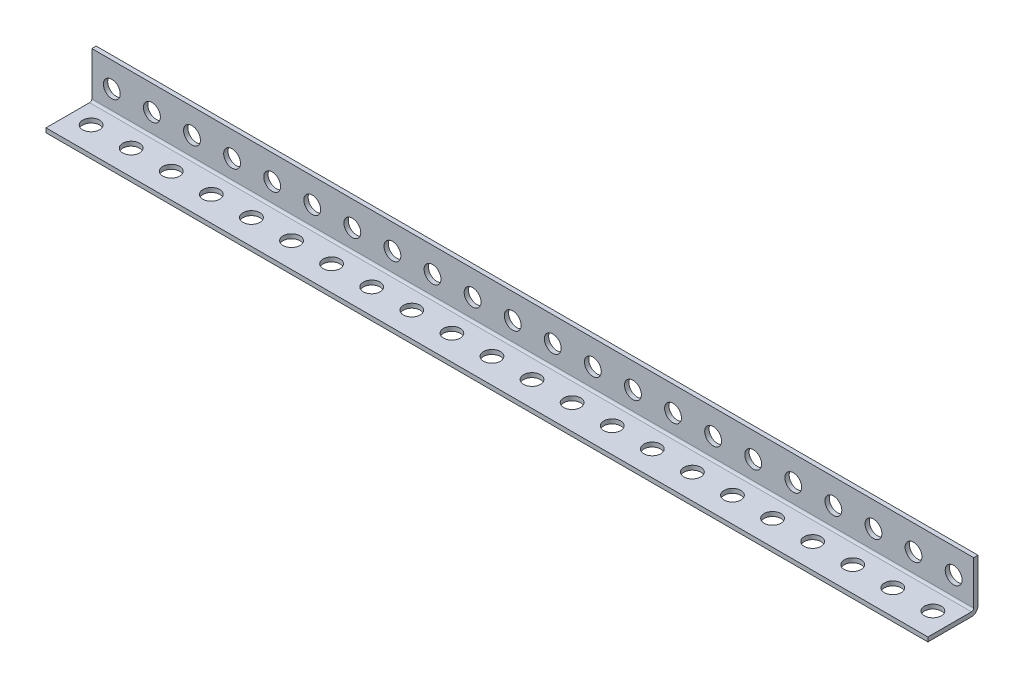
SolidWorks part; units mm, degrees
material "6061-T6 (SS)"
ref_plane "Front Plane" through (0, 0, 0) normal (0, 0, 1) x (1, 0, 0)
ref_plane "Top Plane" through (0, 0, 0) normal (0, 1, 0) x (1, 0, 0)
ref_plane "Right Plane" through (0, 0, 0) normal (1, 0, 0) x (0, 0, -1)
sketch "Sketch1" plane through (0, 0, 0) normal (1, 0, 0) x (0, 0, -1)
  line L0 (-15.875, -13.1318) -> (13.1318, -13.1318) construction
  line L1 (13.1318, -13.1318) -> (13.1318, 15.875) construction
  line L2 (13.1318, 15.875) -> (15.875, 15.875) construction
  line L3 (15.875, 15.875) -> (15.875, -15.875) construction
  line L4 (15.875, -15.875) -> (-15.875, -15.875) construction
  line L5 (-15.875, -15.875) -> (-15.875, -13.1318) construction
  line L6 (0, -15.875) -> (0, 15.875) construction
  line L7 (15.875, 0) -> (-15.875, 0) construction
  dimension "Thickness | T" = 2.7432
  dimension "Width (A)" = 31.75
  dimension "Width (B)" = 31.75
sketch "Sketch2" plane through (0, 0, 0) normal (0, 0, 1) x (1, 0, 0)
  line L0 (-609.6, 0) -> (609.6, 0) construction
  line L1 (-609.6, 15.875) -> (609.6, 15.875) construction
  line L2 (-609.6, 15.875) -> (-609.6, -15.875) construction
  line L3 (-609.6, -15.875) -> (609.6, -15.875) construction
  line L4 (609.6, 15.875) -> (609.6, -15.875) construction
  line L5 (0, 15.875) -> (0, -15.875) construction
  line L7 (-609.6, -13.1318) -> (609.6, -13.1318) construction
  circle A0 centre (596.9, 0) radius 5.334 construction
  circle A1 centre (571.5, 0) radius 5.334 construction
  point P15 (533.4, 0)
  point P16 (-533.4, 0)
  point P24 (602.234, 0)
  dimension "Mounting Hole Diameter" = 10.668
  dimension "Length | L" = 1219.2
  dimension "Mounting Hole Center to Center" = 25.4
  dimension "D1" = 12.7
  dimension "D2" = 63.5
sketch "Sketch3" plane through (0, 0, 0) normal (0, 1, 0) x (1, 0, 0)
  line L1 (-609.6, 15.875) -> (609.6, 15.875) construction
  line L2 (-609.6, 15.875) -> (-609.6, -15.875) construction
  line L3 (-609.6, -15.875) -> (609.6, -15.875) construction
  line L4 (609.6, 15.875) -> (609.6, -15.875) construction
  line L5 (-609.6, 13.1318) -> (609.6, 13.1318) construction
  line L7 (-609.6, 0) -> (609.6, 0) construction
  circle A0 centre (596.9, 0) radius 5.334 construction
  circle A1 centre (571.5, 0) radius 5.334 construction
  point P19 (-533.4, 0)
  point P21 (602.234, 0)
  point P22 (533.4, 0)
sketch "Sketch4" plane through (0, 0, 0) normal (1, 0, 0) x (0, 0, -1)
  line L0 (-15.875, -13.1318) -> (11.7602, -13.1318)
  line L1 (13.1318, -11.7602) -> (13.1318, 15.875)
  line L2 (13.1318, 15.875) -> (15.875, 15.875)
  line L3 (15.875, 15.875) -> (15.875, -11.7602)
  line L4 (11.7602, -15.875) -> (-15.875, -15.875)
  line L5 (-15.875, -15.875) -> (-15.875, -13.1318)
  line L6 (11.7602, -13.1318) -> (11.7602, -10.3886) construction
  arc A0 (11.7602, -13.1318) -> (13.1318, -11.7602) centre (11.7602, -11.7602) ccw
  arc A1 (15.875, -11.7602) -> (11.7602, -15.875) centre (11.7602, -11.7602) cw
extrude "Boss-Extrude1" add sketch "Sketch4" along normal up to vertex (609.6 mm away) and the other way up to vertex (609.6 mm away) up to point (609.6, 0, 0) other way up to point (-609.6, 0, 0)
sketch "Sketch5" plane through (0, 0, 0) normal (0, 0, 1) x (1, 0, 0)
  circle A0 centre (596.9, 0) radius 5.334
extrude "Cut-Extrude1" cut sketch "Sketch5" against normal through all
sketch "Sketch6" plane through (0, 0, 0) normal (0, 1, 0) x (1, 0, 0)
  circle A0 centre (596.9, 0) radius 5.334
extrude "Cut-Extrude2" cut sketch "Sketch6" against normal through all
pattern_linear "LPattern1" count 48 spacing 25.4 along (-1, 0, 0) of "Cut-Extrude2", "Cut-Extrude1"
sketch "Sketch7" plane through (0, 0, -15.875) normal (0, 0, -1) x (-1, 0, 0)
  line L0 (-609.6, -15.875) -> (609.6, -15.875) construction
  line L1 (-609.6, 15.875) -> (25.4, 15.875)
  line L2 (-609.6, 15.875) -> (-609.6, -15.875)
  line L3 (-609.6, -15.875) -> (25.4, -15.875)
  line L4 (25.4, 15.875) -> (25.4, -15.875)
  line L5 (602.234, 0) -> (609.6, 0) construction
  line L6 (609.6, -11.7602) -> (609.6, 15.875) construction
  line L7 (32.766, 0) -> (25.4, 0)
  circle A0 centre (596.9, 0) radius 5.334 construction
  circle A1 centre (38.1, 0) radius 5.334 construction
  dimension "D1" = 7.366
extrude "Cut-Extrude3" cut sketch "Sketch7" against normal blind 70 contours L4 L1 L2 L3
sketch "Sketch8" plane through (0, 0, -15.875) normal (0, 0, -1) x (-1, 0, 0)
  line L0 (25.4, -15.875) -> (609.6, -15.875) construction
  line L1 (25.4, 15.875) -> (50.8, 15.875)
  line L2 (25.4, 15.875) -> (25.4, -15.875)
  line L3 (25.4, -15.875) -> (50.8, -15.875)
  line L4 (50.8, 15.875) -> (50.8, -15.875)
  line L6 (58.166, 0) -> (50.8, 0)
  circle A0 centre (63.5, 0) radius 5.334 construction
  circle M28 centre (38.1, 0) radius 5.334
  line M29 (25.4, 15.875) -> (25.4, -11.7602)
  line M30 (25.4, -11.7602) -> (609.6, -11.7602)
  line M32 (609.6, 15.875) -> (25.4, 15.875)
  dimension "D1" = 7.366
extrude "Cut-Extrude4" cut sketch "Sketch8" against normal blind 70 contours L4 M32 M29 M30 M28 | L4 L2 L3 M30
sketch "Sketch9" plane through (0, 0, -15.875) normal (0, 0, -1) x (-1, 0, 0)
  line L0 (602.234, 0) -> (609.6, 0)
  line L1 (609.6, -11.7602) -> (609.6, 15.875) construction
  line L2 (596.9, 5.334) -> (596.9, 15.875)
  line L3 (50.8, 15.875) -> (609.6, 15.875) construction
  line L4 (58.166, 0) -> (50.8, 0)
  line L5 (50.8, 15.875) -> (50.8, -11.7602) construction
  line L6 (63.5, 5.334) -> (63.5, 15.875)
  circle A0 centre (596.9, 0) radius 5.334 construction
  circle A1 centre (63.5, 0) radius 5.334 construction
sketch "Sketch10" plane through (0, -15.875, 0) normal (0, -1, 0) x (1, 0, 0)
  line L0 (-58.166, 0) -> (-50.8, 0)
  line L1 (-50.8, 15.875) -> (-50.8, -11.7602) construction
  line L2 (-63.5, 5.334) -> (-63.5, 15.875)
  line L3 (-50.8, 15.875) -> (-609.6, 15.875) construction
  line L4 (-602.234, 0) -> (-609.6, 0)
  line L5 (-609.6, 15.875) -> (-609.6, -11.7602) construction
  line L6 (-596.9, 5.334) -> (-596.9, 15.875)
  circle A0 centre (-63.5, 0) radius 5.334 construction
  circle A1 centre (-596.9, 0) radius 5.334 construction
equation "\"D1@Sketch2\"= ( \"Length | L@Sketch2\" - \"Mounting Hole Center to Center@Sketch2\" * \"Num Holes\" ) / 2"
equation "\"Num Holes\"= int ( \"Length | L@Sketch2\" / \"Mounting Hole Center to Center@Sketch2\" ) - 1"
equation "\"D2@Sketch2\"=\"Mounting Hole Center to Center@Sketch2\"*2.5"
equation "\"D3@LPattern1\"=\"Mounting Hole Center to Center@Sketch2\""
